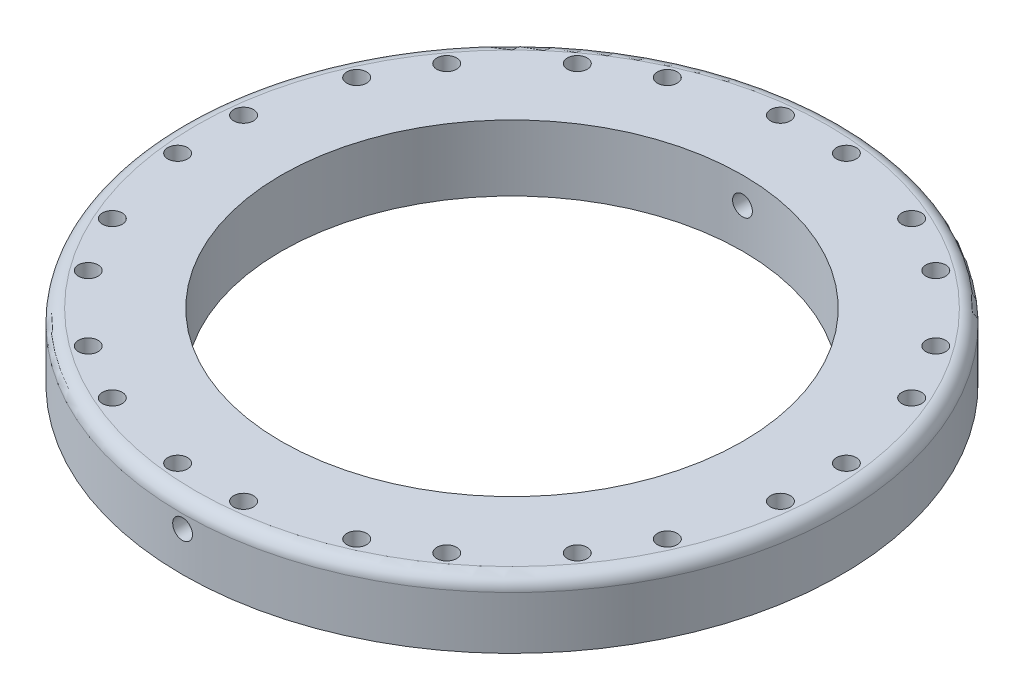
SolidWorks part; units mm, degrees
ref_plane "Přední rovina" through (0, 0, 0) normal (0, 0, 1) x (1, 0, 0)
ref_plane "Horní rovina" through (0, 0, 0) normal (0, 1, 0) x (1, 0, 0)
ref_plane "Pravá rovina" through (0, 0, 0) normal (1, 0, 0) x (0, 0, -1)
sketch "Skica1" plane through (0, 0, 0) normal (0, 1, 0) x (1, 0, 0)
  circle A0 centre (0, 0) radius 250
  dimension "D1" = 500
extrude "Přidat vysunutím1" add sketch "Skica1" against normal blind 50
sketch "Skica2" plane through (0, 0, 0) normal (0, 1, 0) x (1, 0, 0)
  circle A0 centre (0, 0) radius 175
  dimension "D1" = 350
extrude "Odebrat vysunutím1" cut sketch "Skica2" against normal blind 60
fillet "Zaoblit1" radius 10 1 edges at (0, 0, 250)
sketch "Skica4" plane through (0, 0, 0) normal (0, 1, 0) x (1, 0, 0)
  line L0 (0, 250) -> (0, -250) construction
  circle A0 centre (-25, -228.6373) radius 7.5
  circle A2 centre (0, 0) radius 250 construction
  circle A3 centre (0, 0) radius 240 construction
  circle A4 centre (25, -228.6373) radius 7.5
  circle A5 centre (-135.9693, -185.5057) radius 7.5
  circle A6 centre (-92.668, -210.5057) radius 7.5
  circle A7 centre (-210.5057, -92.668) radius 7.5
  circle A8 centre (-185.5057, -135.9693) radius 7.5
  circle A9 centre (-228.6373, 25) radius 7.5
  circle A10 centre (-228.6373, -25) radius 7.5
  circle A11 centre (-185.5057, 135.9693) radius 7.5
  circle A12 centre (-210.5057, 92.668) radius 7.5
  circle A13 centre (-92.668, 210.5057) radius 7.5
  circle A14 centre (-135.9693, 185.5057) radius 7.5
  circle A15 centre (25, 228.6373) radius 7.5
  circle A16 centre (-25, 228.6373) radius 7.5
  circle A17 centre (135.9693, 185.5057) radius 7.5
  circle A18 centre (92.668, 210.5057) radius 7.5
  circle A19 centre (210.5057, 92.668) radius 7.5
  circle A20 centre (185.5057, 135.9693) radius 7.5
  circle A21 centre (228.6373, -25) radius 7.5
  circle A22 centre (228.6373, 25) radius 7.5
  circle A23 centre (185.5057, -135.9693) radius 7.5
  circle A24 centre (210.5057, -92.668) radius 7.5
  circle A25 centre (92.668, -210.5057) radius 7.5
  circle A26 centre (135.9693, -185.5057) radius 7.5
  point P58 (0, 0)
  dimension "D1" = 15
  dimension "D2" = 25
  dimension "D3" = 230
  dimension "D4" = 12
extrude "Odebrat vysunutím2" cut sketch "Skica4" against normal through all
sketch "Skica6" plane through (0, 0, 0) normal (0, 0, 1) x (1, 0, 0)
  line L1 (-250, -50) -> (250, -50) construction
  circle A0 centre (0, -20) radius 7.5
  dimension "D1" = 15
  dimension "D2" = 30
extrude "Odebrat vysunutím3" cut sketch "Skica6" against normal through all both and the other way through all
